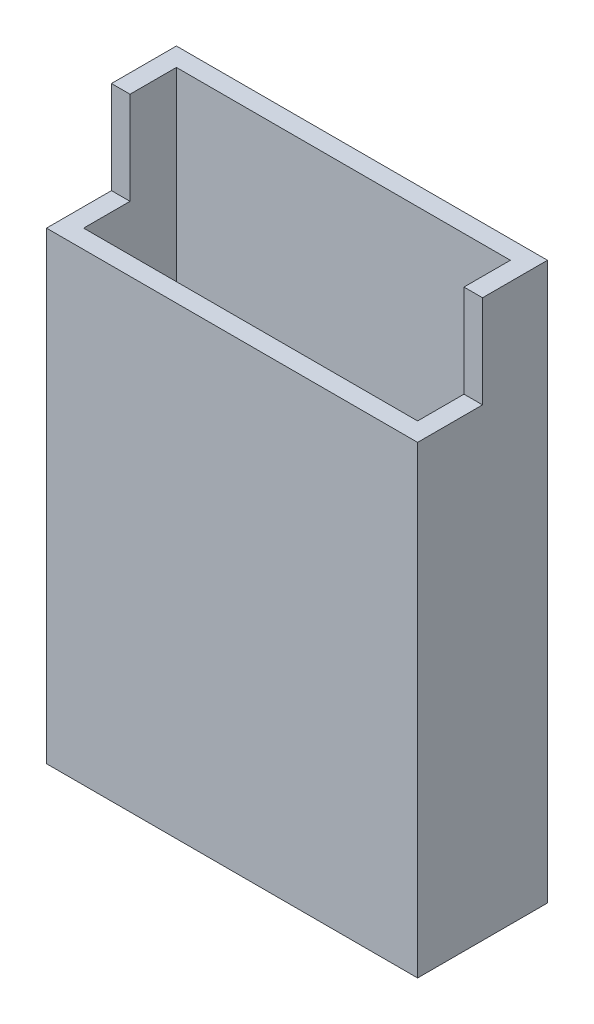
SolidWorks part; units mm, degrees
ref_plane "前视基准面" through (0, 0, 0) normal (0, 0, 1) x (1, 0, 0)
ref_plane "上视基准面" through (0, 0, 0) normal (0, 1, 0) x (1, 0, 0)
ref_plane "右视基准面" through (0, 0, 0) normal (1, 0, 0) x (0, 0, -1)
sketch "草图1" plane through (0, 0, 0) normal (0, 1, 0) x (1, 0, 0)
  line L1 (0, 14) -> (40, 14)
  line L2 (0, 14) -> (0, 0)
  line L3 (0, 0) -> (40, 0)
  line L4 (40, 14) -> (40, 0)
extrude "凸台-拉伸1" add sketch "草图1" along normal blind 60 contours L1 L4 L3 L2
sketch "草图6" plane through (0, 60, 0) normal (0, 1, 0) x (1, 0, 0)
  line L1 (2, 2) -> (38, 2)
  line L2 (2, 2) -> (2, 12)
  line L3 (2, 12) -> (38, 12)
  line L4 (38, 2) -> (38, 12)
extrude "切除-拉伸2" cut sketch "草图6" against normal blind 55 contours L3 L4 L1 L2
sketch "草图7" plane through (0, 0, 0) normal (0, 0, 1) x (1, 0, 0)
  line L0 (40, 60) -> (40, 0) construction
  line L1 (0, 60) -> (40, 60)
  line L2 (0, 60) -> (0, 50)
  line L3 (0, 50) -> (40, 50)
  line L4 (40, 60) -> (40, 50)
extrude "切除-拉伸3" cut sketch "草图7" against normal blind 7
